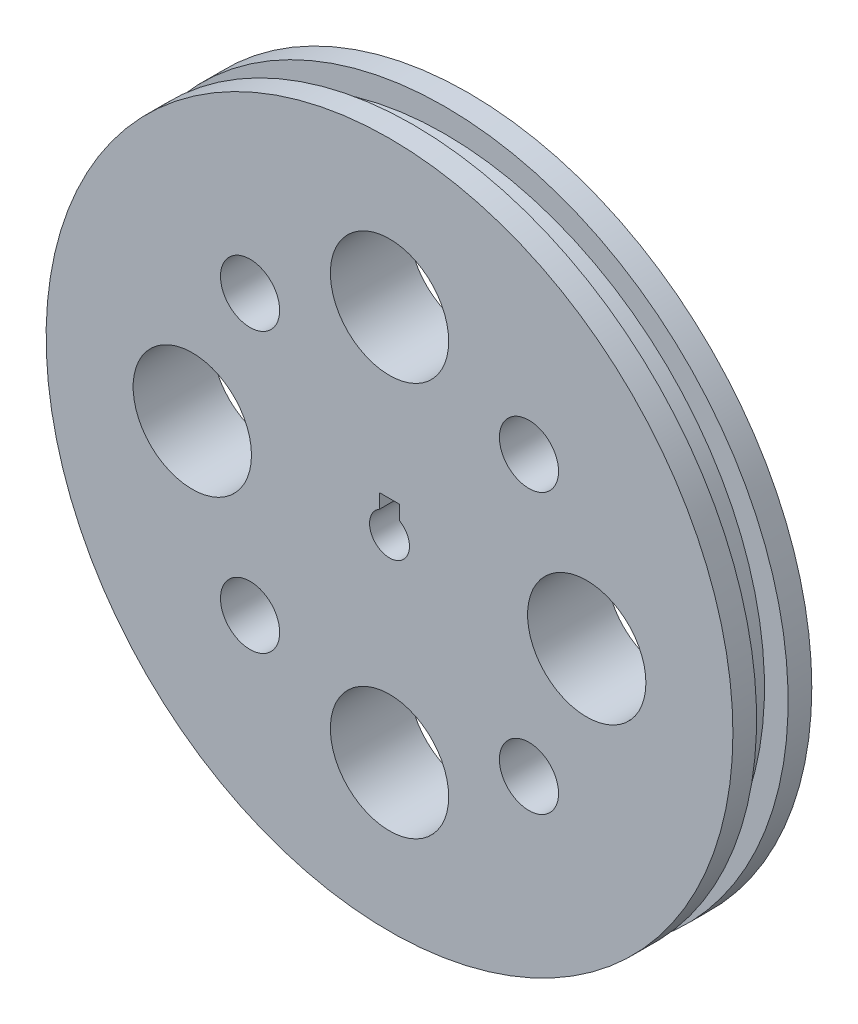
SolidWorks part; units mm, degrees
ref_plane "Front Plane" through (0, 0, 0) normal (0, 0, 1) x (1, 0, 0)
ref_plane "Top Plane" through (0, 0, 0) normal (0, 1, 0) x (1, 0, 0)
ref_plane "Right Plane" through (0, 0, 0) normal (1, 0, 0) x (0, 0, -1)
sketch "Sketch1" plane through (0, 0, 0) normal (0, 0, 1) x (1, 0, 0)
  circle A0 centre (0, 0) radius 110.5678
extrude "Boss-Extrude1" add sketch "Sketch1" along normal blind 25.4
sketch "Sketch2" plane through (0, 0, 25.4) normal (0, 0, 1) x (1, 0, 0)
  line L0 (-110.5678, 0) -> (110.5678, 0) construction
  line L1 (0, 110.5678) -> (0, -110.5678) construction
  line L2 (0, 0) -> (-78.1832, 78.1832) construction
  line L3 (0, 0) -> (78.1832, 78.1832) construction
  line L4 (0, 0) -> (78.1832, -78.1832) construction
  line L5 (0, 0) -> (-78.1832, -78.1832) construction
  circle A0 centre (0, 0) radius 110.5678 construction
  circle A1 centre (0, 0) radius 63.5 construction
  circle A2 centre (0, 63.5) radius 19.05
  circle A3 centre (63.5, 0) radius 19.05
  circle A4 centre (44.9013, -44.9013) radius 9.525
  circle A5 centre (0, -63.5) radius 19.05
  circle A6 centre (44.9013, 44.9013) radius 9.525
  circle A7 centre (-44.9013, -44.9013) radius 9.525
  circle A8 centre (-63.5, 0) radius 19.05
  circle A9 centre (-44.9013, 44.9013) radius 9.525
  point P33 (0, 0)
  dimension "D1" = 38.1
  dimension "D2" = 63.5
  dimension "D3" = 45
  dimension "D7" = 4
  dimension "D11" = 19.05
  dimension "D4" = 45
  dimension "D5" = 45
  dimension "D6" = 45
extrude "Cut-Extrude3" cut sketch "Sketch2" against normal blind 140.716
sketch "Sketch5" plane through (0, 0, 25.4) normal (0, 0, 1) x (1, 0, 0)
  line L1 (-3.175, 10.16) -> (3.175, 10.16)
  line L2 (-3.175, 10.16) -> (-3.175, 5.588)
  line L4 (3.175, 10.16) -> (3.175, 5.588)
  arc A0 (-3.175, 5.588) -> (3.175, 5.588) centre (0, 0) ccw
  dimension "D1" = 3.175
  dimension "D2" = 6.35
  dimension "D3" = 10.16
extrude "Cut-Extrude4" cut sketch "Sketch5" against normal blind 134.112
sketch "Sketch6" plane through (0, 0, 0) normal (1, 0, 0) x (0, 0, -1)
  line L0 (0, 110.5678) -> (-25.4, 110.5678) construction
  line L1 (-17.78, 110.5678) -> (-7.62, 110.5678)
  line L2 (-17.78, 110.5678) -> (-17.78, 102.9478)
  line L3 (-17.78, 102.9478) -> (-7.62, 102.9478)
  line L4 (-7.62, 110.5678) -> (-7.62, 102.9478)
  line L5 (0, -110.5678) -> (0, 110.5678) construction
  line L6 (-25.4, 110.5678) -> (-25.4, -110.5678) construction
  line L7 (0, 0) -> (-25.4, 0) construction
  dimension "D1" = 7.62
  dimension "D2" = 7.62
  dimension "D3" = 7.62
revolve "Cut-Revolve1" cut sketch "Sketch6" angle 360 about L7
